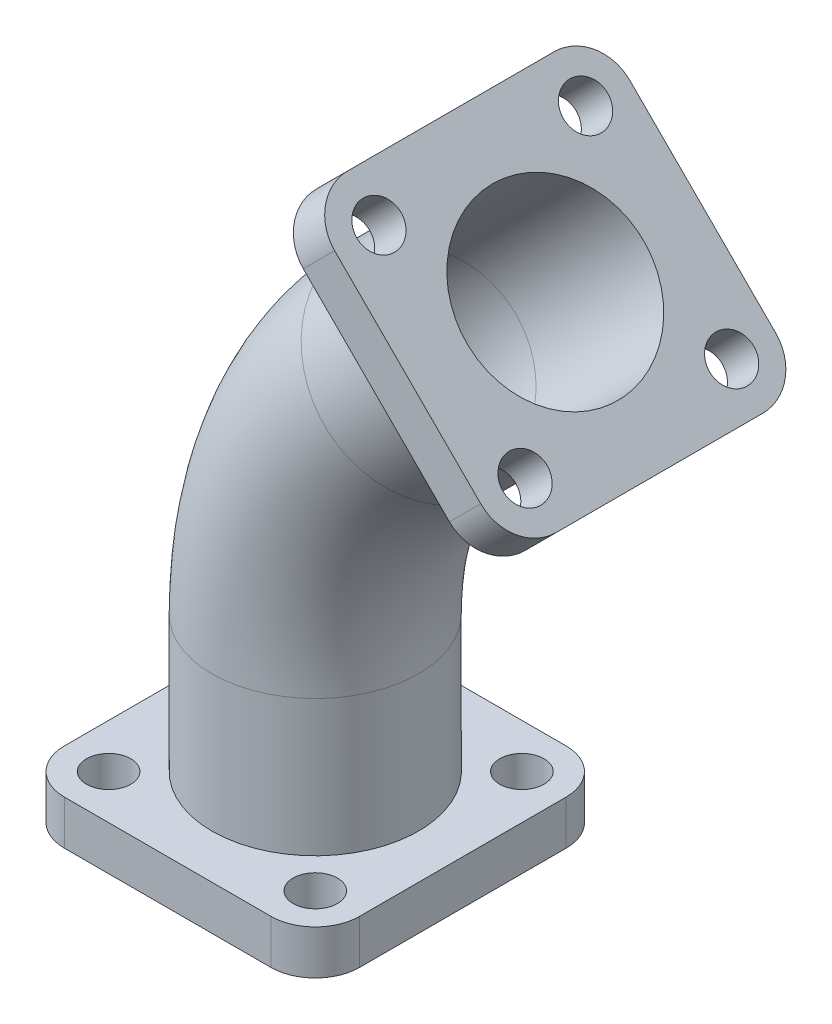
SolidWorks part; units mm, degrees
ref_plane "Front Plane" through (0, 0, 0) normal (0, 0, 1) x (1, 0, 0)
ref_plane "Top Plane" through (0, 0, 0) normal (0, 1, 0) x (1, 0, 0)
ref_plane "Right Plane" through (0, 0, 0) normal (1, 0, 0) x (0, 0, -1)
sketch "Sketch1" plane through (0, 0, 0) normal (0, 1, 0) x (1, 0, 0)
  line L1 (35, -50) -> (-35, -50)
  line L2 (50, -35) -> (50, 35)
  line L3 (35, 50) -> (-35, 50)
  line L4 (-50, -35) -> (-50, 35)
  line L5 (50, -50) -> (-50, 50) construction
  line L6 (50, 50) -> (-50, -50) construction
  arc A0 (50, 35) -> (35, 50) centre (35, 35) ccw
  arc A1 (50, -35) -> (35, -50) centre (35, -35) cw
  arc A2 (-35, -50) -> (-50, -35) centre (-35, -35) cw
  arc A3 (-50, 35) -> (-35, 50) centre (-35, 35) cw
  circle A5 centre (0, 0) radius 30
  point P0 (0, 0)
  dimension "D3" = 15
  dimension "D1" = 100
  dimension "D2" = 100
extrude "Boss-Extrude1" add sketch "Sketch1" along normal blind 15
sketch "Sketch2" plane through (0, 15, 0) normal (0, 1, 0) x (1, 0, 0)
  circle A0 centre (-35, 35) radius 7.5
  circle A1 centre (35, 35) radius 7.5
  circle A2 centre (35, -35) radius 7.5
  circle A3 centre (-35, -35) radius 7.5
extrude "Cut-Extrude1" cut sketch "Sketch2" against normal blind 15
sketch "Sketch4" plane through (0, 15, 0) normal (0, 1, 0) x (1, 0, 0)
  circle A0 centre (0, 0) radius 30
  circle A1 centre (0, 0) radius 35
sketch "Sketch5" plane through (0, 0, 0) normal (0, 0, 1) x (1, 0, 0)
  line L0 (0, 15) -> (0, 61.1522)
  line L1 (35, 15) -> (-35, 15) construction
  line L2 (38.0761, 153.0761) -> (70.7107, 185.7107)
  arc A0 (38.0761, 153.0761) -> (0, 61.1522) centre (130, 61.1522) ccw
  point P8 (0, 115)
  dimension "D4" = 130
  dimension "D1" = 100
  dimension "D2" = 100
  dimension "D3" = 135
sweep "Sweep1" add profiles "Sketch4" path "Sketch5"
sketch "Sketch6" plane through (128.2107, 128.2107, 0) normal (0.7071, 0.7071, 0) x (0, 0, -1)
  line L1 (35, 31.3173) -> (-35, 31.3173)
  line L2 (50, 46.3173) -> (50, 116.3173)
  line L3 (35, 131.3173) -> (-35, 131.3173)
  line L4 (-50, 46.3173) -> (-50, 116.3173)
  line L5 (50, 31.3173) -> (-50, 131.3173) construction
  line L6 (50, 131.3173) -> (-50, 31.3173) construction
  arc A0 (35, 131.3173) -> (50, 116.3173) centre (35, 116.3173) cw
  arc A1 (50, 46.3173) -> (35, 31.3173) centre (35, 46.3173) cw
  arc A2 (-50, 46.3173) -> (-35, 31.3173) centre (-35, 46.3173) ccw
  arc A3 (-50, 116.3173) -> (-35, 131.3173) centre (-35, 116.3173) cw
  point P0 (0, 81.3173)
  dimension "D3" = 15
  dimension "D1" = 100
  dimension "D2" = 100
extrude "Boss-Extrude2" add sketch "Sketch6" along normal blind 15
sketch "Sketch7" plane through (138.8173, 138.8173, 0) normal (0.7071, 0.7071, 0) x (0, 0, -1)
  circle A0 centre (-35, 116.3173) radius 7.5
  circle A1 centre (35, 116.3173) radius 7.5
  circle A2 centre (35, 46.3173) radius 7.5
  circle A3 centre (-35, 46.3173) radius 7.5
  circle A4 centre (0, 81.3173) radius 30
  dimension "D1" = 15
extrude "Cut-Extrude2" cut sketch "Sketch7" against normal blind 15
